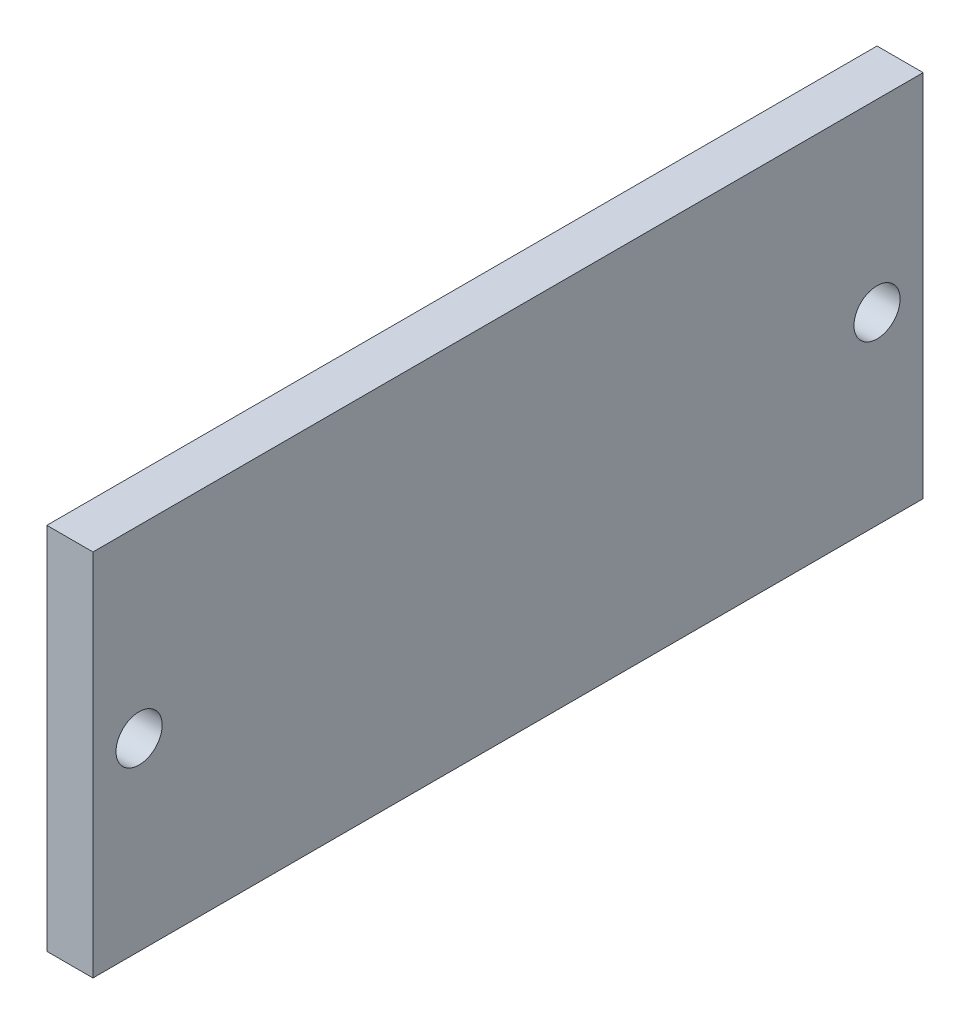
SolidWorks part; units mm, degrees
material "PET"
ref_plane "Front Plane" through (0, 0, 0) normal (0, 0, 1) x (1, 0, 0)
ref_plane "Top Plane" through (0, 0, 0) normal (0, 1, 0) x (1, 0, 0)
ref_plane "Right Plane" through (0, 0, 0) normal (1, 0, 0) x (0, 0, -1)
sketch "Sketch1" plane through (0, 0, 0) normal (1, 0, 0) x (0, 0, -1)
  line L1 (0, 0) -> (457.2, 0)
  line L2 (0, 0) -> (0, 203.2)
  line L3 (0, 203.2) -> (457.2, 203.2)
  line L4 (457.2, 0) -> (457.2, 203.2)
  dimension "D1" = 457.2
  dimension "D2" = 203.2
extrude "Boss-Extrude1" add sketch "Sketch1" along normal mid plane 25.4
sketch "Sketch2" plane through (-12.7, 0, 0) normal (-1, 0, 0) x (0, 0, 1)
  circle A6 centre (-431.8, 101.6) radius 12.7
ref_plane "Plane2" through (0, 0, -228.6) normal (0, 0, 1) x (1, 0, 0)
extrude "Cut-Extrude1" cut sketch "Sketch2" against normal through all both and the other way through all
mirror "Mirror3" about plane through (0, 0, -228.6) normal (0, 0, 1) of "Cut-Extrude1"
